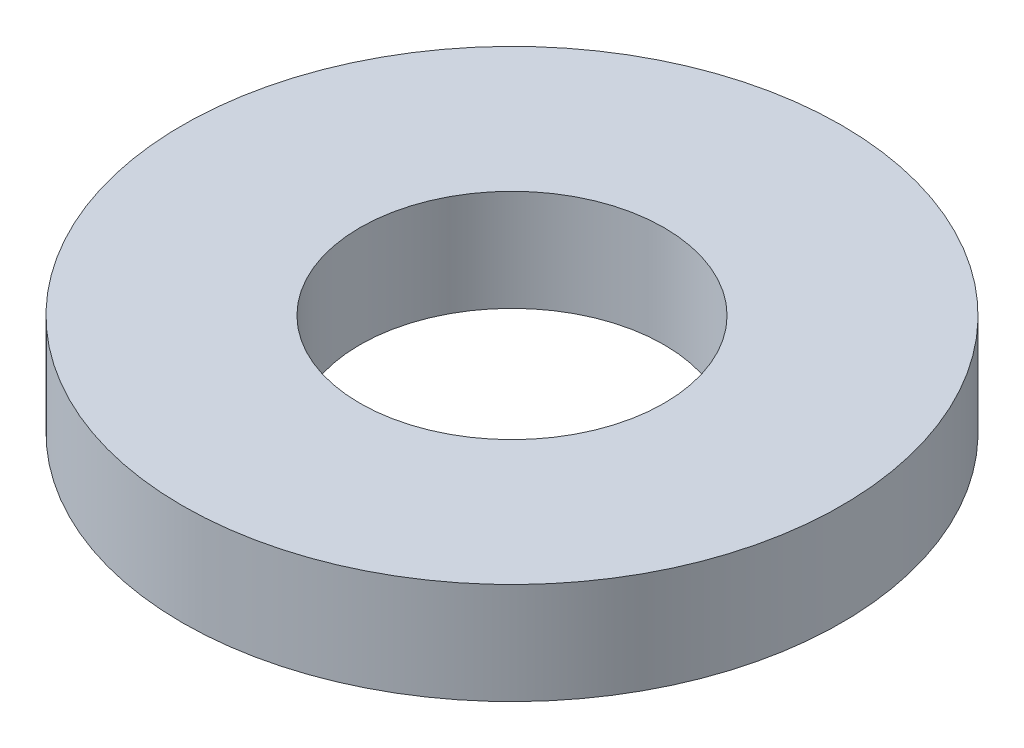
SolidWorks part; units mm, degrees
ref_plane "Front Plane" through (0, 0, 0) normal (0, 0, 1) x (1, 0, 0)
ref_plane "Top Plane" through (0, 0, 0) normal (0, 1, 0) x (1, 0, 0)
ref_plane "Right Plane" through (0, 0, 0) normal (1, 0, 0) x (0, 0, -1)
sketch "Sketch1" plane through (0, 0, 0) normal (0, 1, 0) x (1, 0, 0)
  circle A0 centre (0, 0) radius 3
  circle A1 centre (0, 0) radius 6.5
  dimension "D1" = 13
  dimension "D2" = 6
extrude "Boss-Extrude1" add sketch "Sketch1" along normal blind 2
